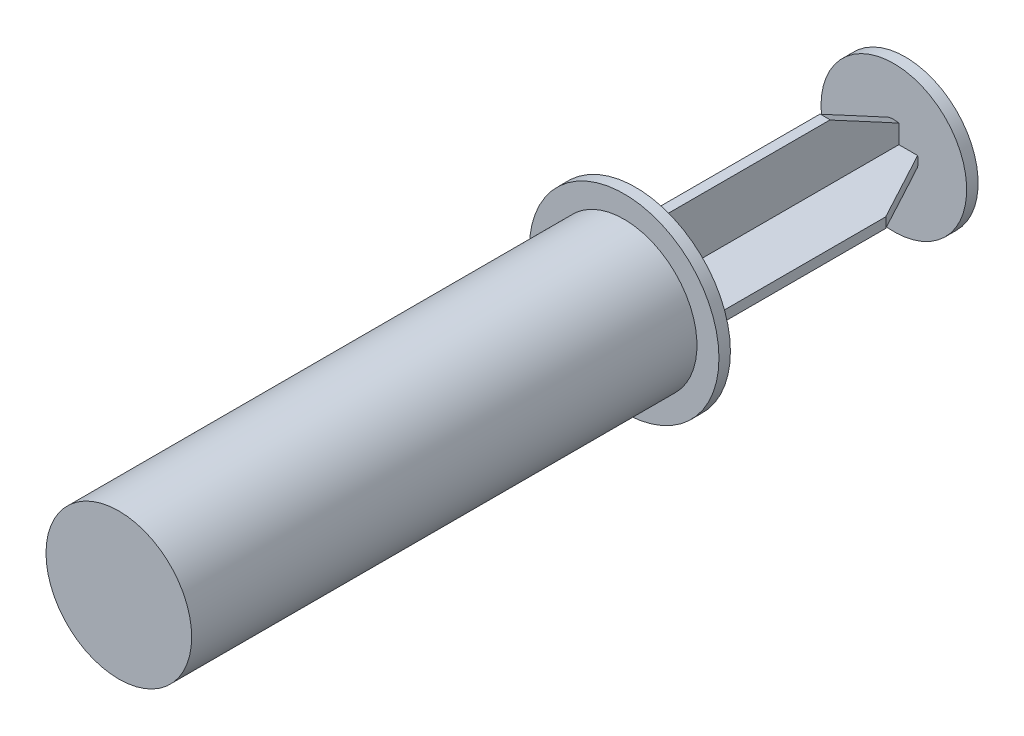
SolidWorks part; units mm, degrees
ref_plane "Front Plane" through (0, 0, 0) normal (0, 0, 1) x (1, 0, 0)
ref_plane "Top Plane" through (0, 0, 0) normal (0, 1, 0) x (1, 0, 0)
ref_plane "Right Plane" through (0, 0, 0) normal (1, 0, 0) x (0, 0, -1)
sketch "Sketch1" plane through (0, 0, 0) normal (0, 0, 1) x (1, 0, 0)
  circle A0 centre (0, 0) radius 15.9
  dimension "D1" = 31.8
extrude "Boss-Extrude1" add sketch "Sketch1" along normal blind 110.3
sketch "Sketch4" plane through (0, 0, 0) normal (0, 0, -1) x (-1, 0, 0)
  circle A0 centre (0, 0) radius 20.7
  dimension "D1" = 41.4
extrude "Boss-Extrude4" add sketch "Sketch4" along normal blind 2.5
sketch "Sketch2" plane through (0, 0, -2.5) normal (0, 0, -1) x (-1, 0, 0)
  line L0 (1.1, -13.3) -> (-1.1, -13.3)
  line L1 (1.1, -13.3) -> (1.1, 13.3)
  line L2 (1.1, 13.3) -> (-1.1, 13.3)
  line L3 (-1.1, -13.3) -> (-1.1, 13.3)
  line L4 (1.1, -13.3) -> (-1.1, 13.3) construction
  line L5 (1.1, 13.3) -> (-1.1, -13.3) construction
  line L6 (13.3, 1.1) -> (-13.3, 1.1)
  line L7 (13.3, 1.1) -> (13.3, -1.1)
  line L8 (13.3, -1.1) -> (-13.3, -1.1)
  line L9 (-13.3, 1.1) -> (-13.3, -1.1)
  line L10 (13.3, 1.1) -> (-13.3, -1.1) construction
  line L11 (13.3, -1.1) -> (-13.3, 1.1) construction
  point P8 (0, 0)
  dimension "D1" = 26.6
  dimension "D2" = 26.6
  dimension "D3" = 2.2
  dimension "D4" = 2.2
extrude "Boss-Extrude2" add sketch "Sketch2" along normal blind 56.375 contours L6 L1 L2 L3 | L8 L1 L6 L3 | L1 L8 L3 L0 | L8 L7 L6 L1 | L6 L9 L8 L3
sketch "Sketch3" plane through (0, 0, -58.875) normal (0, 0, -1) x (-1, 0, 0)
  circle A0 centre (0, 0) radius 15.9
  circle A2 centre (0, 0) radius 15.9 construction
extrude "Boss-Extrude3" add sketch "Sketch3" along normal blind 2.5
ref_axis "Axis1" through (0, 0, 121.7025) along (0, 0, -1)
ref_plane "Plane1" through (0, 0, 0) normal (1, 0, 0) x (0, 0, -1)
sketch "Sketch5" plane through (0, 0, 0) normal (1, 0, 0) x (0, 0, -1)
  line L0 (43.875, 13.3) -> (58.875, 5.3)
  line L1 (58.875, 13.3) -> (2.5, 13.3) construction
  line L3 (58.875, 1.1) -> (58.875, 13.3) construction
  line L4 (43.875, 13.3) -> (58.875, 13.3)
  line L5 (58.875, 13.3) -> (58.875, 5.3)
  line L7 (43.875, 13.3) -> (58.875, 13.3)
  line L8 (43.875, 13.3) -> (43.875, 14.9512)
  line L9 (43.875, 14.9512) -> (58.875, 14.9512)
  line L10 (58.875, 13.3) -> (58.875, 14.9512)
  dimension "D1" = 8
  dimension "D2" = 15
revolve "Cut-Revolve4" cut sketch "Sketch5" angle 360 about axis through (0, 0, 121.7025) along (0, 0, -1)
